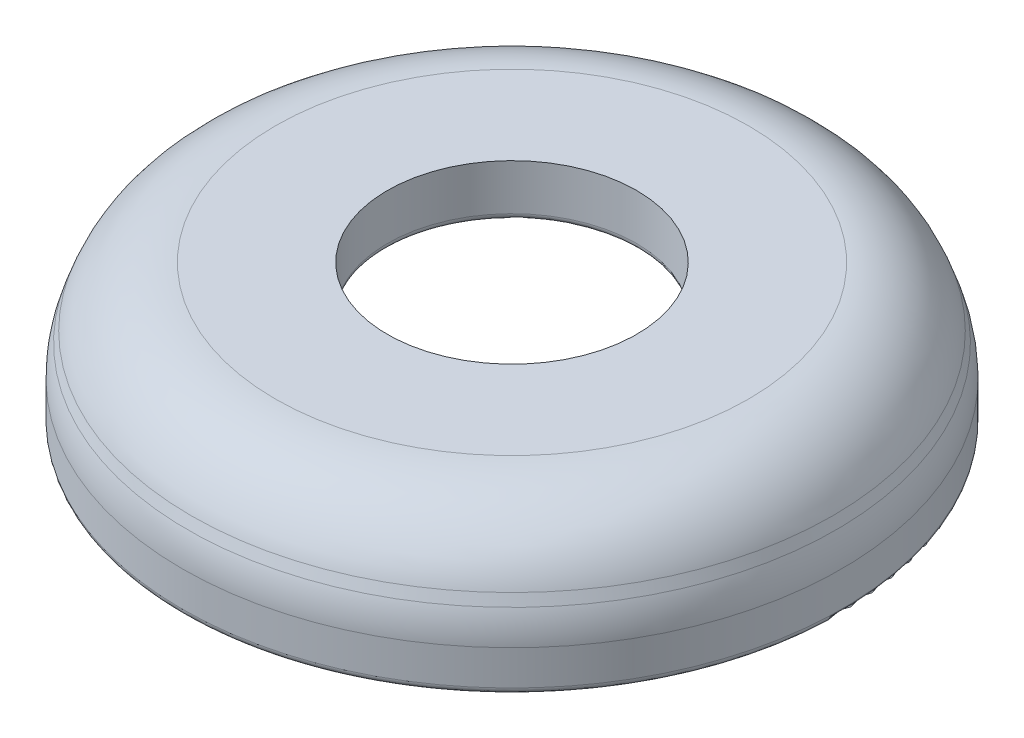
SolidWorks part; units mm, degrees
ref_plane "Front Plane" through (0, 0, 0) normal (0, 0, 1) x (1, 0, 0)
ref_plane "Top Plane" through (0, 0, 0) normal (0, 1, 0) x (1, 0, 0)
ref_plane "Right Plane" through (0, 0, 0) normal (1, 0, 0) x (0, 0, -1)
sketch "Sketch1" plane through (0, 0, 0) normal (0, 0, 1) x (1, 0, 0)
  line L0 (0, -4.9933) -> (0, 13.2631) construction
  line L1 (4.75, 4.25) -> (9.0162, 4.25)
  line L5 (9.75, 2.25) -> (5, 2.25)
  line L6 (4.75, 2.5) -> (4.75, 4.25)
  line L7 (0, 2.25) -> (9.75, 2.25) construction
  line L8 (9.75, 2.25) -> (12.5, -5.5) construction
  line L9 (12.5, -5.5) -> (0, -5.5) construction
  line L10 (0, -5.5) -> (0, 2.25) construction
  line L11 (10.0836, 2.0144) -> (11.1529, -0.9991)
  line L12 (11.3885, -1.1655) -> (12.307, -1.1655)
  line L13 (12.3526, 1.6006) -> (12.2138, 1.9917)
  line L14 (12.557, -0.9155) -> (12.557, 0.4135)
  line L15 (13.2158, -0.8319) -> (12.3526, 1.6006) construction
  line L16 (12.557, -1.1655) -> (12.9801, -1.1655) construction
  arc A2 (12.2138, 1.9917) -> (9.0162, 4.25) centre (9.0162, 0.8571) ccw
  arc A3 (9.75, 2.25) -> (10.0836, 2.0144) centre (9.75, 1.896) cw
  arc A4 (5, 2.25) -> (4.75, 2.5) centre (5, 2.5) cw
  arc A5 (11.1529, -0.9991) -> (11.3885, -1.1655) centre (11.3885, -0.9155) ccw
  arc A6 (12.9801, -1.1655) -> (13.2158, -0.8319) centre (12.9801, -0.9155) ccw construction
  arc A7 (12.557, 0.4135) -> (12.3526, 1.6006) centre (9.0072, 0.4135) ccw
  arc A8 (12.557, -0.9155) -> (12.307, -1.1655) centre (12.307, -0.9155) cw
  point P18 (4.75, 2.25)
  dimension "D5" = 4.25
  dimension "D3" = 0.25
  dimension "D9" = 0.25
  dimension "D1" = 4.75
  dimension "D2" = 7.75
  dimension "D4" = 2
  dimension "D6" = 2
  dimension "D7" = 9.75
  dimension "D8" = 12.5
revolve "Revolve1" add sketch "Sketch1" angle 360 about L0
